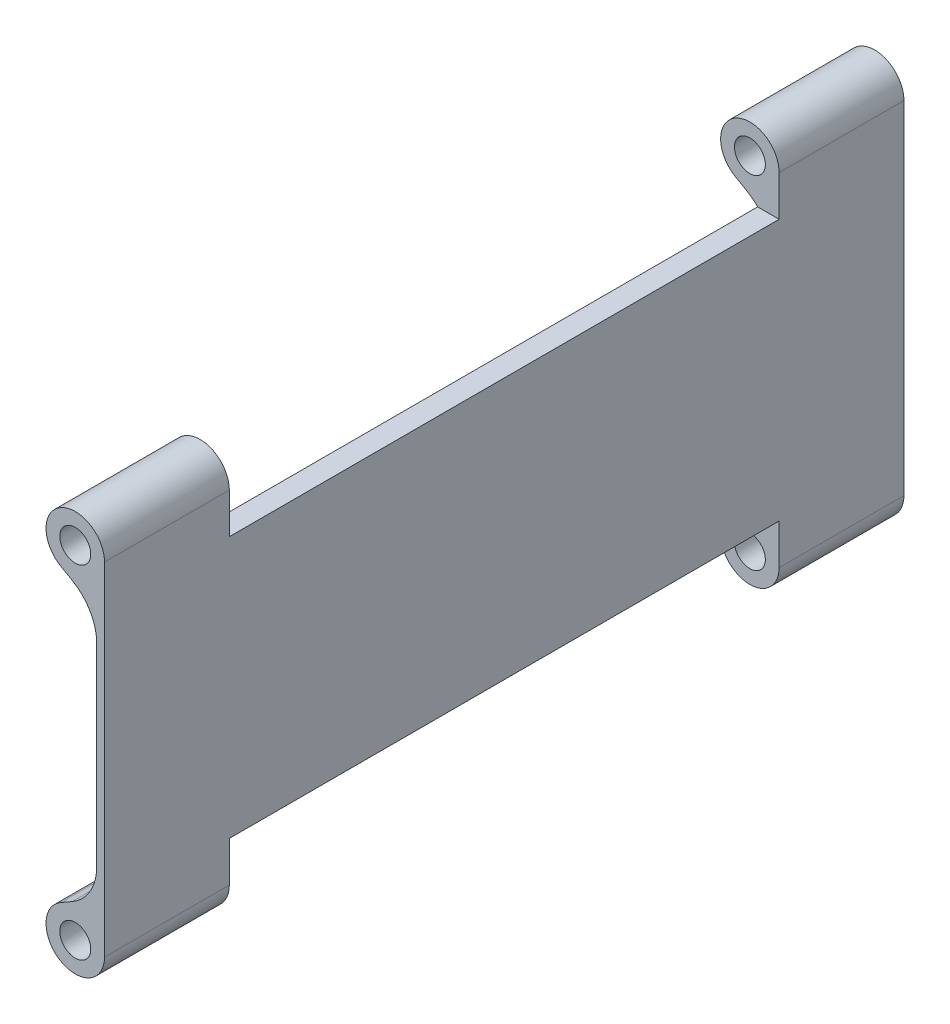
SolidWorks part; units mm, degrees
material "ABS"
ref_plane "Alzado" through (0, 0, 0) normal (0, 0, 1) x (1, 0, 0)
ref_plane "Planta" through (0, 0, 0) normal (0, 1, 0) x (1, 0, 0)
ref_plane "Vista lateral" through (0, 0, 0) normal (1, 0, 0) x (0, 0, -1)
sketch "Croquis1" plane through (0, 0, 0) normal (0, 0, 1) x (1, 0, 0)
  line L5 (-13.465, 0) -> (13.8234, 0) construction
  line L8 (-1.6, 25.6462) -> (-8.9869, 29.8863)
  line L9 (-1.6, 25.6462) -> (-1.6, -25.6462)
  line L10 (0, 35.09) -> (0, -35.09)
  line L11 (-1.6, -25.6462) -> (-8.9869, -29.8863)
  circle A0 centre (-6, 35.09) radius 3.175
  arc A5 (0, 35.09) -> (-8.9869, 29.8863) centre (-6, 35.09) ccw
  arc A6 (0, -35.09) -> (-8.9869, -29.8863) centre (-6, -35.09) cw
  circle A7 centre (-6, -35.09) radius 3.175
  point P7 (0, 0)
  point P15 (0, 0)
  point P16 (-1.6, 0)
  point P17 (-1.6, 0)
  dimension "D1" = 6.35
  dimension "D2" = 70.18
  dimension "D3" = 1.6
  dimension "D4" = 6
extrude "Saliente-Extruir1" add sketch "Croquis1" against normal blind 164
fillet "Redondeo1" radius 10 2 edges at (-1.6, -25.6462, -82) (-1.6, 25.6462, -82)
sketch "Croquis3" plane through (0, 0, 0) normal (1, 0, 0) x (0, 0, -1)
  line L0 (0, 0) -> (164, 0) construction
  line L1 (25.6041, 44.9478) -> (138.3959, 44.9478)
  line L2 (25.6041, 44.9478) -> (25.6041, 26.8024)
  line L3 (25.6041, 26.8024) -> (138.3959, 26.8024)
  line L4 (138.3959, 44.9478) -> (138.3959, 26.8024)
  line L5 (138.3959, -44.9478) -> (138.3959, -26.8024)
  line L6 (25.6041, -26.8024) -> (138.3959, -26.8024)
  line L7 (25.6041, -44.9478) -> (25.6041, -26.8024)
  line L8 (25.6041, -44.9478) -> (138.3959, -44.9478)
  line L9 (164, 19.8559) -> (164, -19.8559) construction
  point P16 (82, 0)
  point P17 (82, -26.8024)
extrude "Cortar-Extruir2" cut sketch "Croquis3" against normal through all
